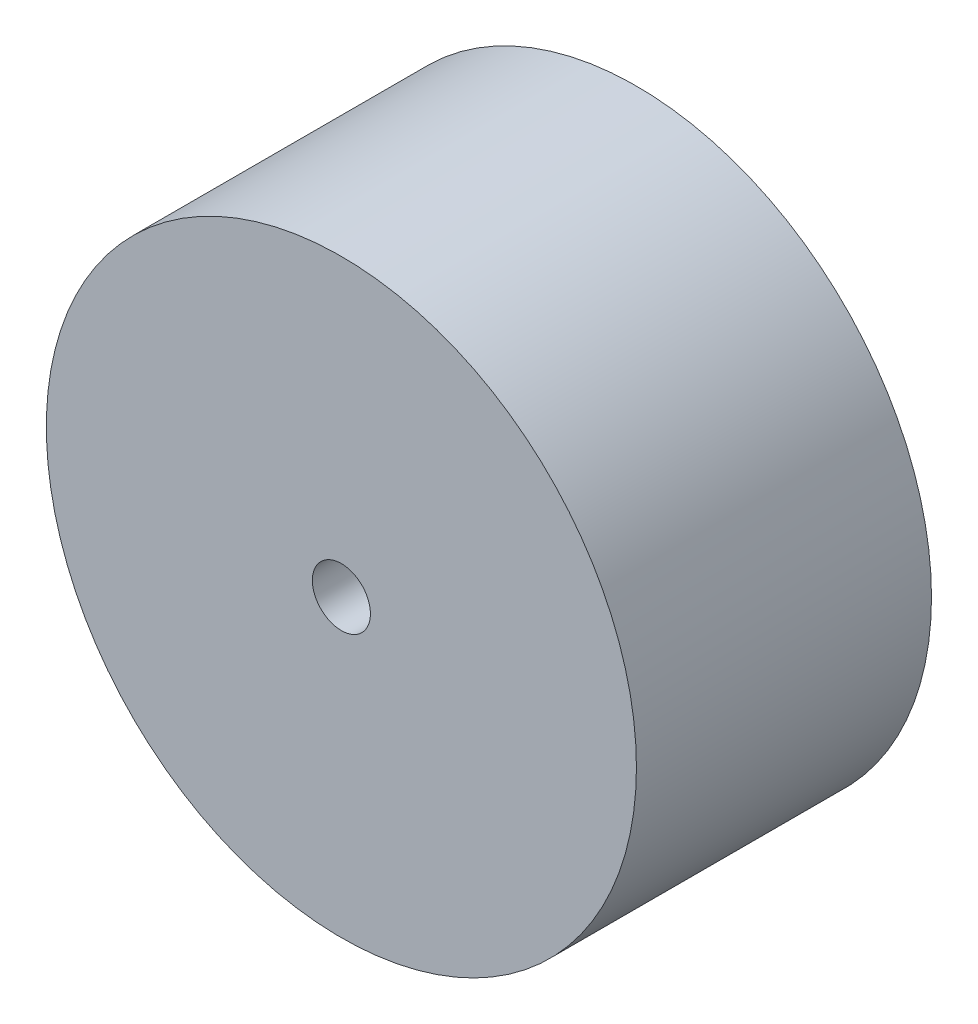
SolidWorks part; units mm, degrees
material "Silicon Rubber"
ref_plane "Front Plane" through (0, 0, 0) normal (0, 0, 1) x (1, 0, 0)
ref_plane "Top Plane" through (0, 0, 0) normal (0, 1, 0) x (1, 0, 0)
ref_plane "Right Plane" through (0, 0, 0) normal (1, 0, 0) x (0, 0, -1)
sketch "Sketch2" plane through (0, 0, 0) normal (0, 0, 1) x (1, 0, 0)
  circle A0 centre (0, 0) radius 25.4
  circle A1 centre (0, 0) radius 2.5
  dimension "D1" = 50.8
  dimension "D2" = 5
extrude "Boss-Extrude1" add sketch "Sketch2" along normal blind 25.4
